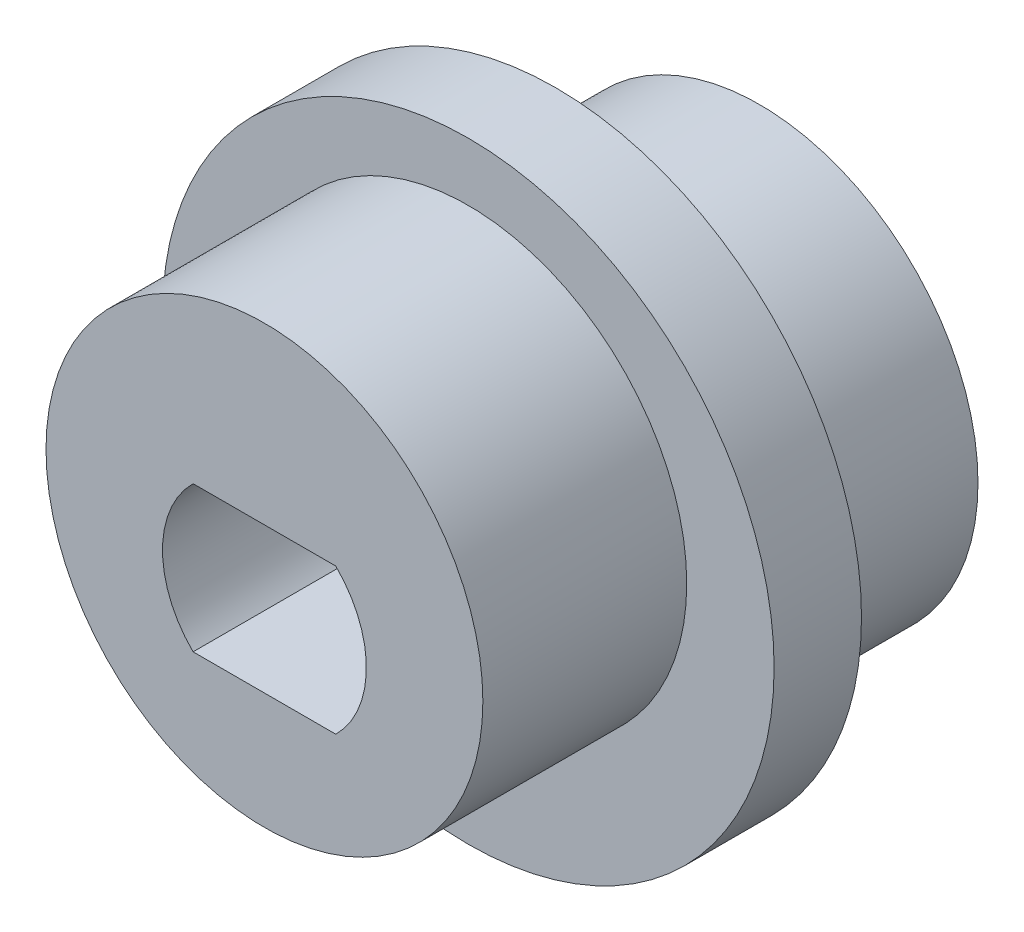
SolidWorks part; units mm, degrees
ref_plane "Front Plane" through (0, 0, 0) normal (0, 0, 1) x (1, 0, 0)
ref_plane "Top Plane" through (0, 0, 0) normal (0, 1, 0) x (1, 0, 0)
ref_plane "Right Plane" through (0, 0, 0) normal (1, 0, 0) x (0, 0, -1)
sketch "Sketch1" plane through (0, 0, 0) normal (0, 0, 1) x (1, 0, 0)
  circle A0 centre (0, 0) radius 7.5
  dimension "D1" = 15
extrude "Boss-Extrude1" add sketch "Sketch1" along normal blind 7
sketch "Sketch2" plane through (0, 0, 7) normal (0, 0, 1) x (1, 0, 0)
  circle A0 centre (0, 1) radius 8.5
  circle A1 centre (0, 0) radius 7.5 construction
  dimension "D1" = 17
  dimension "D2" = 1
extrude "Boss-Extrude2" add sketch "Sketch2" along normal blind 3
sketch "Sketch3" plane through (0, 0, 10) normal (0, 0, 1) x (1, 0, 0)
  circle A0 centre (0, 2) radius 7.5
  circle A1 centre (0, 1) radius 8.5 construction
  dimension "D1" = 15
  dimension "D2" = 1
extrude "Boss-Extrude3" add sketch "Sketch3" along normal blind 7
sketch "Sketch6" plane through (0, 0, 10) normal (0, 0, 1) x (1, 0, 0)
  line L0 (0, -1.5) -> (0, 3.5)
  line L1 (-2.4495, 3.5) -> (2.4495, 3.5)
  line L2 (-2.4495, -1.5) -> (2.4495, -1.5)
  arc A0 (-2.4495, 3.5) -> (-2.4495, -1.5) centre (0, 1) ccw
  arc A1 (2.4495, -1.5) -> (2.4495, 3.5) centre (0, 1) ccw
  point P7 (0, 1)
  point P10 (0, 3.5)
  point P13 (0, -1.5)
  dimension "D1" = 7
  dimension "D2" = 5
extrude "Cut-Extrude3" cut sketch "Sketch6" against normal through all both and the other way through all contours A0 L2 A1 L1
sketch "Sketch7" plane through (0, 0, 10) normal (0, 0, 1) x (1, 0, 0)
  circle A0 centre (0, 1) radius 8.5
  circle A1 centre (0, 1) radius 10.5
  circle A2 centre (0, 1) radius 8.5 construction
  dimension "D1" = 2
extrude "Boss-Extrude4" add sketch "Sketch7" against normal up to surface (3 mm away) up to face at (8, 0.5, 7)
